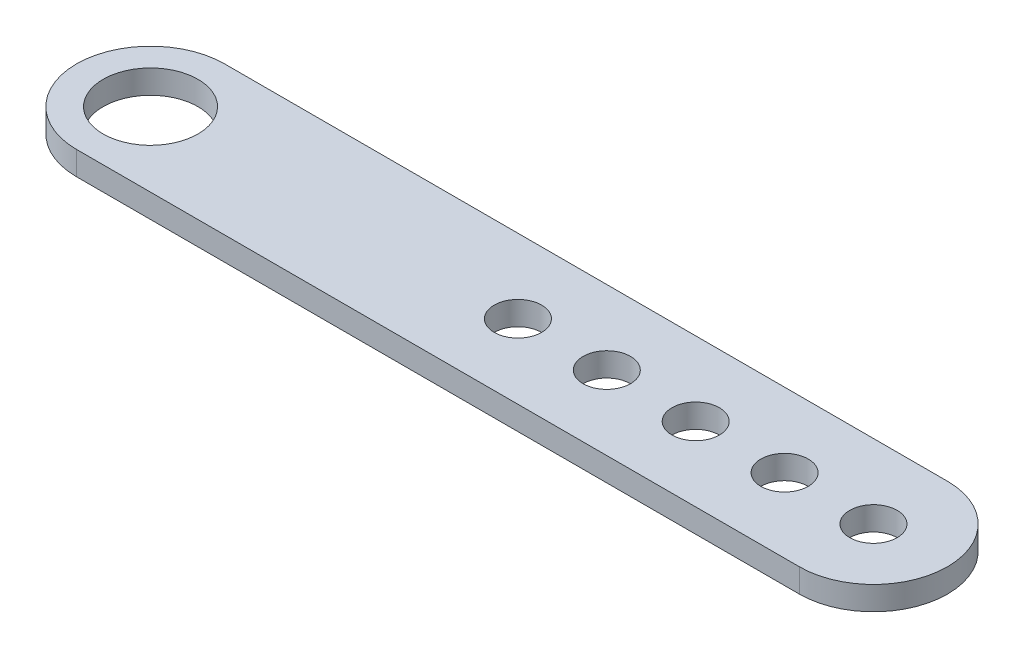
SolidWorks part; units mm, degrees
material "1023 Carbon Steel Sheet (SS)"
ref_plane "Front Plane" through (0, 0, 0) normal (0, 0, 1) x (1, 0, 0)
ref_plane "Top Plane" through (0, 0, 0) normal (0, 1, 0) x (1, 0, 0)
ref_plane "Right Plane" through (0, 0, 0) normal (1, 0, 0) x (0, 0, -1)
sketch "Sketch1" plane through (0, 0, 0) normal (0, 1, 0) x (1, 0, 0)
  line L0 (-61, 0) -> (61, 0) construction
  line L1 (-61, 12.5) -> (61, 12.5)
  line L2 (-61, -12.5) -> (61, -12.5)
  arc A0 (-61, 12.5) -> (-61, -12.5) centre (-61, 0) ccw
  arc A1 (61, -12.5) -> (61, 12.5) centre (61, 0) ccw
  circle A2 centre (-61, 0) radius 8
  circle A3 centre (1, 0) radius 4
  circle A8 centre (16, 0) radius 4
  circle A9 centre (31, 0) radius 4
  circle A10 centre (46, 0) radius 4
  circle A11 centre (61, 0) radius 4
  point P3 (0, 0)
  dimension "D1" = 16
  dimension "D2" = 12.5
  dimension "D4" = 8
  dimension "D3" = 62
  dimension "D5" = 122
  dimension "D6" = 5
extrude "Boss-Extrude1" add sketch "Sketch1" along normal mid plane 4
